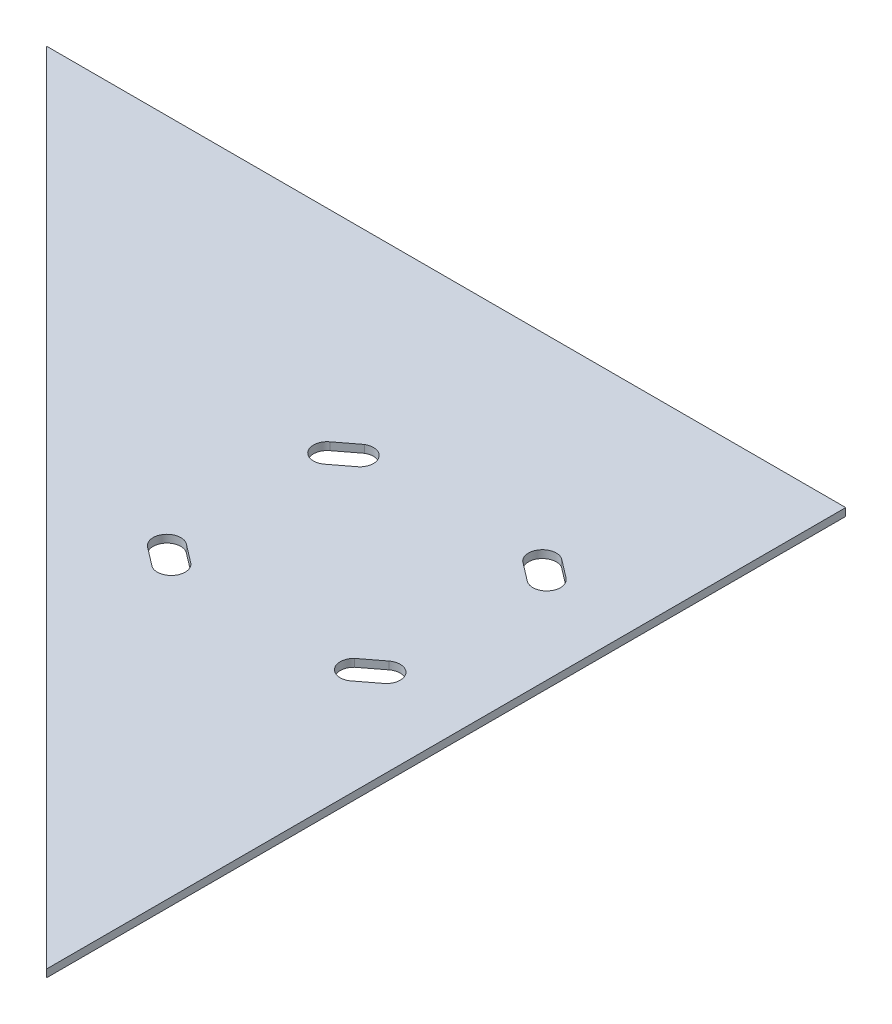
SolidWorks part; units mm, degrees
ref_plane "Front Plane" through (0, 0, 0) normal (0, 0, 1) x (1, 0, 0)
ref_plane "Top Plane" through (0, 0, 0) normal (0, 1, 0) x (1, 0, 0)
ref_plane "Right Plane" through (0, 0, 0) normal (1, 0, 0) x (0, 0, -1)
sketch "Sketch1" plane through (0, 0, 0) normal (0, 1, 0) x (1, 0, 0)
  line L0 (-69.85, 0) -> (69.85, 0) construction
  line L1 (69.85, 50.8) -> (-69.85, 50.8) construction
  line L2 (69.85, 50.8) -> (69.85, -50.8) construction
  line L3 (69.85, -50.8) -> (-69.85, -50.8) construction
  line L4 (-69.85, 50.8) -> (-69.85, -50.8) construction
  line L5 (69.85, 50.8) -> (-69.85, -50.8) construction
  line L6 (69.85, -50.8) -> (-69.85, 50.8) construction
  line L7 (0, 50.8) -> (0, -50.8) construction
  line L8 (-52.07, 50.8) -> (-52.07, -50.8) construction
  line L9 (52.07, 50.8) -> (52.07, -50.8) construction
  line L10 (-30.48, 50.8) -> (-30.48, -50.8) construction
  line L11 (30.48, 50.8) -> (30.48, -50.8) construction
  line L12 (-69.85, 27.94) -> (69.85, 27.94) construction
  line L13 (-69.85, 44.45) -> (69.85, 44.45) construction
  line L14 (-52.07, 27.94) -> (-30.48, 44.45) construction
  line L15 (-52.07, 44.45) -> (-30.48, 27.94) construction
  line L16 (-33.2043, 42.3667) -> (-49.3457, 30.0233) construction
  line L17 (-45.8741, 25.4836) -> (-29.7327, 37.8269) construction
  line L18 (-45.8741, 25.4836) -> (-52.8173, 34.5631) construction
  line L19 (-29.7327, 37.8269) -> (-36.6759, 46.9064) construction
  line L20 (-52.8173, 34.5631) -> (-36.6759, 46.9064) construction
  line L21 (-45.8741, 25.4836) -> (-36.6759, 46.9064) construction
  line L22 (-29.7327, 37.8269) -> (-52.8173, 34.5631) construction
  line L23 (-40.7112, 43.8206) -> (-33.7681, 34.7411) construction
  line L24 (-48.7819, 37.6489) -> (-41.8388, 28.5694) construction
  line L25 (-48.7819, 37.6489) -> (-40.7112, 43.8206)
  line L26 (-33.7681, 34.7411) -> (-41.8388, 28.5694)
  line L27 (33.7681, 34.7411) -> (41.8388, 28.5694)
  line L28 (48.7819, 37.6489) -> (40.7112, 43.8206)
  line L29 (33.7681, -34.7411) -> (41.8388, -28.5694)
  line L30 (48.7819, -37.6489) -> (40.7112, -43.8206)
  line L31 (-48.7819, -37.6489) -> (-40.7112, -43.8206)
  line L32 (-33.7681, -34.7411) -> (-41.8388, -28.5694)
  line L33 (81.28, -209.55) -> (81.28, 120.65)
  line L34 (81.28, 120.65) -> (-248.92, 120.65)
  line L35 (81.28, -209.55) -> (-248.92, 120.65)
  line L36 (81.28, 95.25) -> (-223.52, 95.25) construction
  line L37 (55.88, 120.65) -> (55.88, -184.15) construction
  line L38 (81.28, -173.629) -> (-212.999, 120.65) construction
  arc A0 (-40.7112, 43.8206) -> (-33.7681, 34.7411) centre (-37.7756, 38.871) cw
  arc A1 (-48.7819, 37.6489) -> (-41.8388, 28.5694) centre (-45.3103, 33.1092) ccw
  arc A2 (48.7819, 37.6489) -> (41.8388, 28.5694) centre (45.3103, 33.1092) cw
  arc A3 (40.7112, 43.8206) -> (33.7681, 34.7411) centre (37.7756, 38.871) ccw
  arc A4 (48.7819, -37.6489) -> (41.8388, -28.5694) centre (45.3103, -33.1092) ccw
  arc A5 (40.7112, -43.8206) -> (33.7681, -34.7411) centre (37.7756, -38.871) cw
  arc A6 (-48.7819, -37.6489) -> (-41.8388, -28.5694) centre (-45.3103, -33.1092) cw
  arc A7 (-40.7112, -43.8206) -> (-33.7681, -34.7411) centre (-37.7756, -38.871) ccw
  point P0 (0, 0)
  point P26 (-41.275, 36.195)
  point P30 (-41.275, 36.195)
  dimension "D1" = 101.6
  dimension "D2" = 139.7
  dimension "D3" = 17.78
  dimension "D4" = 17.78
  dimension "D5" = 39.37
  dimension "D6" = 22.86
  dimension "D7" = 6.35
  dimension "D8" = 20.32
  dimension "D9" = 11.43
  dimension "D10" = 5.08
  dimension "D11" = 5.08
  dimension "D12" = 330.2
  dimension "D13" = 69.85
  dimension "D14" = 11.43
  dimension "D16" = 29.21
  dimension "D17" = 25.4
extrude "Boss-Extrude1" add sketch "Sketch1" along normal blind 3.175 contours L1 L4 L3 L2 A7 L31 A6 L32 A1 L25 A0 L26 A3 L28 A2 L27 L30 A5 L29 A4
